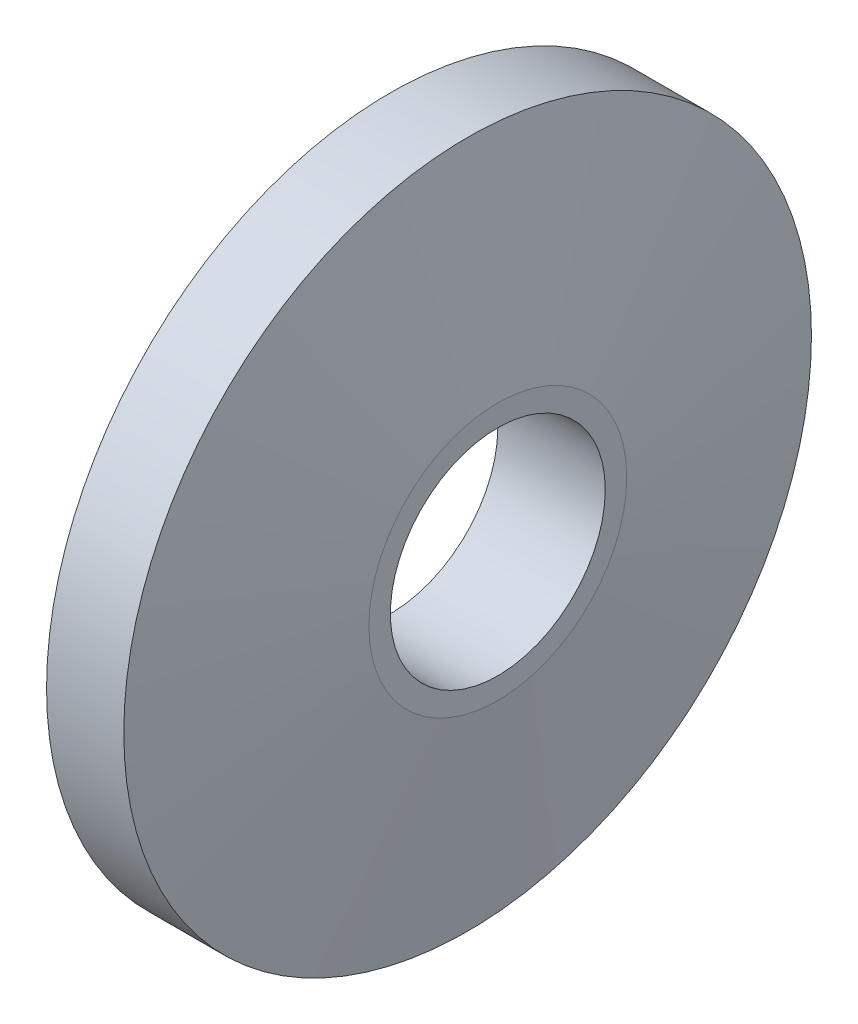
SolidWorks part; units mm, degrees
ref_plane "Front Plane" through (0, 0, 0) normal (0, 0, 1) x (1, 0, 0)
ref_plane "Top Plane" through (0, 0, 0) normal (0, 1, 0) x (1, 0, 0)
ref_plane "Right Plane" through (0, 0, 0) normal (1, 0, 0) x (0, 0, -1)
sketch "Sketch1" plane through (0, 0, 0) normal (0, 0, 1) x (1, 0, 0)
  line L0 (-13.2766, 0) -> (17.0213, 0) construction
  line L3 (0, 0) -> (0, 8)
  line L7 (2.5, 3) -> (2.5, 0)
  line L8 (2.5, 0) -> (0, 0)
  line L9 (0, 8) -> (1.7973, 8)
  line L10 (1.7973, 8) -> (2.5, 3)
  dimension "D1" = 8
  dimension "D2" = 2.5
  dimension "D3" = 5
  dimension "D4" = 172
revolve "Revolve1" add sketch "Sketch1" angle 360 about L0
sketch "Sketch2" plane through (2.5, 0, 0) normal (1, 0, 0) x (0, 0, -1)
  line L2 (-0.25, 2.2361) -> (-0.25, 2.4861)
  line L3 (-0.25, 2.4861) -> (0.25, 2.4861)
  line L4 (0.25, 2.2361) -> (0.25, 2.4861)
  line L5 (0, 2.25) -> (0.25, 2.4861) construction
  line L6 (-0.25, 2.4861) -> (0, 2.25) construction
  arc A0 (-0.25, 2.2361) -> (0.25, 2.2361) centre (0, 0) ccw
  point P3 (0, 2.25)
  dimension "D1" = 4.5
  dimension "D2" = 0.5
  dimension "D3" = 0.25
  dimension "D4" = 0.0139
extrude "Cut-Extrude1" [suppressed] cut sketch "Sketch2" against normal through all
sketch "Sketch5" plane through (2.5, 0, 0) normal (1, 0, 0) x (0, 0, -1)
  circle A0 centre (0, 0) radius 2.5
  dimension "D1" = 5
extrude "Cut-Extrude3" cut sketch "Sketch5" against normal through all
sketch "Sketch4" plane through (2.5, 0, 0) normal (1, 0, 0) x (0, 0, -1)
  circle A0 centre (0, 0) radius 3
  dimension "D1" = 6
extrude "Cut-Extrude2" [suppressed] cut sketch "Sketch4" against normal blind 0.5
